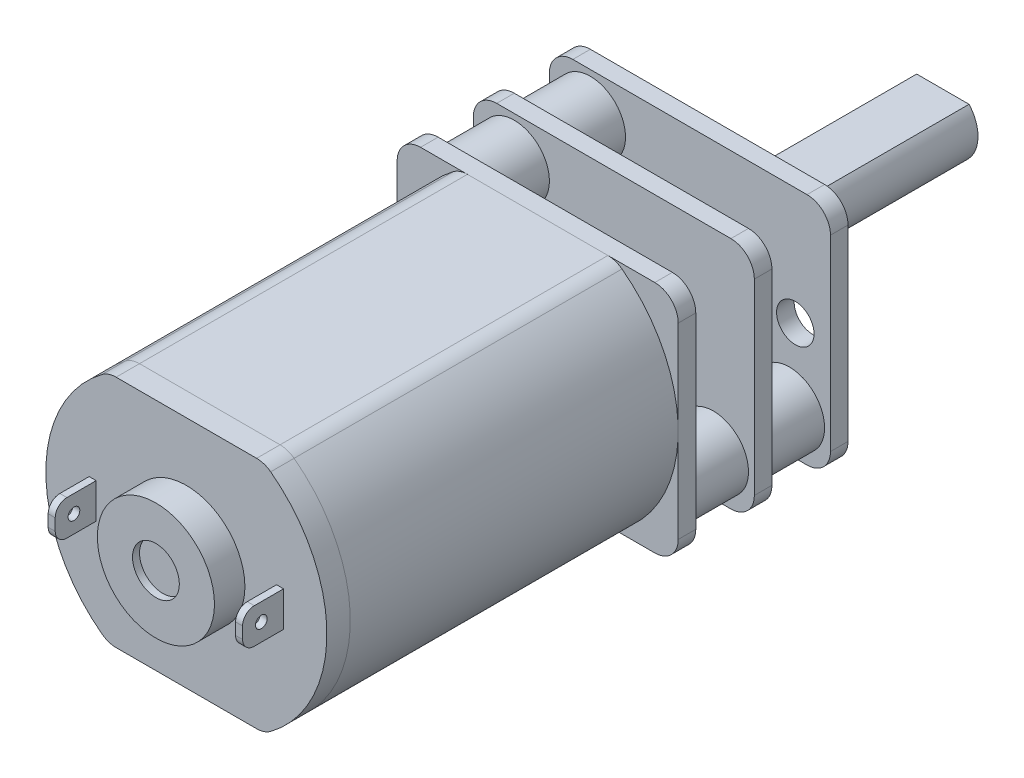
SolidWorks part; units mm, degrees
ref_plane "Front Plane" through (0, 0, 0) normal (0, 0, 1) x (1, 0, 0)
ref_plane "Top Plane" through (0, 0, 0) normal (0, 1, 0) x (1, 0, 0)
ref_plane "Right Plane" through (0, 0, 0) normal (1, 0, 0) x (0, 0, -1)
sketch "Sketch1" plane through (0, 0, 0) normal (0, 0, 1) x (1, 0, 0)
  line L0 (-6, 0) -> (6, 0) construction
  line L1 (-3.3166, -5) -> (3.3166, -5)
  line L2 (-3.3166, 5) -> (3.3166, 5)
  line L4 (-6, 5) -> (6, 5) construction
  line L5 (-6, -5) -> (6, -5) construction
  arc A0 (-3.3166, 5) -> (-3.3166, -5) centre (0, 0) ccw
  arc A1 (3.3166, -5) -> (3.3166, 5) centre (0, 0) ccw
  dimension "D1" = 12
  dimension "D2" = 5
  dimension "D3" = 5
extrude "Boss-Extrude1" add sketch "Sketch1" against normal blind 14
fillet "Fillet1" radius 1 4 edges at (3.3166, -5, -7) (-3.3166, -5, -7) (3.3166, 5, -7) (-3.3166, 5, -7)
sketch "Sketch2" plane through (0, 0, 0) normal (0, 0, 1) x (1, 0, 0)
  line L2 (-3, -5) -> (3, -5)
  line L3 (3, 5) -> (-3, 5)
  line L4 (-3, -5) -> (3, -5)
  line L5 (3, 5) -> (-3, 5)
  arc A6 (3, -5) -> (3.6, -4.8) centre (3, -4) ccw
  arc A7 (3.6, -4.8) -> (3.6, 4.8) centre (0, 0) ccw
  arc A8 (3.6, 4.8) -> (3, 5) centre (3, 4) ccw
  arc A9 (-3, 5) -> (-3.6, 4.8) centre (-3, 4) ccw
  arc A10 (-3.6, 4.8) -> (-3.6, -4.8) centre (0, 0) ccw
  arc A11 (-3.6, -4.8) -> (-3, -5) centre (-3, -4) ccw
  arc A12 (3, -5) -> (3.6, -4.8) centre (3, -4) ccw
  arc A13 (3.6, -4.8) -> (3.6, 4.8) centre (0, 0) ccw
  arc A14 (3.6, 4.8) -> (3, 5) centre (3, 4) ccw
  arc A15 (-3, 5) -> (-3.6, 4.8) centre (-3, 4) ccw
  arc A16 (-3.6, 4.8) -> (-3.6, -4.8) centre (0, 0) ccw
  arc A17 (-3.6, -4.8) -> (-3, -5) centre (-3, -4) ccw
  dimension "D1" = 0
extrude "Boss-Extrude2" add sketch "Sketch2" along normal blind 1 separate body
sketch "Sketch3" plane through (0, 0, 1) normal (0, 0, 1) x (1, 0, 0)
  circle A0 centre (0, 0) radius 2.5
  dimension "D1" = 5
extrude "Boss-Extrude3" add sketch "Sketch3" along normal blind 1.3
sketch "Sketch4" plane through (0, 0, 2.3) normal (0, 0, 1) x (1, 0, 0)
  circle A0 centre (0, 0) radius 1
  dimension "D1" = 2
extrude "Cut-Extrude1" cut sketch "Sketch4" against normal blind 0.3
sketch "Sketch5" plane through (0, 0, 1) normal (0, 0, 1) x (1, 0, 0)
  line L0 (-6, 0) -> (6, 0) construction
  line L1 (0, 5) -> (0, -5) construction
  line L2 (-4.15, 0.75) -> (-3.85, 0.75)
  line L3 (-4.15, 0.75) -> (-4.15, -0.75)
  line L4 (-4.15, -0.75) -> (-3.85, -0.75)
  line L5 (-3.85, 0.75) -> (-3.85, -0.75)
  line L6 (-4.15, 0.75) -> (-3.85, -0.75) construction
  line L7 (-4.15, -0.75) -> (-3.85, 0.75) construction
  line L8 (3, 5) -> (-3, 5) construction
  line L9 (-3, -5) -> (3, -5) construction
  line L10 (4.15, -0.75) -> (3.85, 0.75) construction
  line L11 (4.15, 0.75) -> (3.85, -0.75) construction
  line L12 (3.85, 0.75) -> (3.85, -0.75)
  line L13 (4.15, -0.75) -> (3.85, -0.75)
  line L14 (4.15, 0.75) -> (4.15, -0.75)
  line L15 (4.15, 0.75) -> (3.85, 0.75)
  arc A0 (-3.6, 4.8) -> (-3.6, -4.8) centre (0, 0) ccw construction
  arc A1 (3.6, -4.8) -> (3.6, 4.8) centre (0, 0) ccw construction
  point P8 (-4, 0)
  point P13 (-4, 0.75)
  point P20 (0, 0)
  point P25 (4, 0)
  dimension "D1" = 1.5
  dimension "D2" = 0.3
  dimension "D3" = 4
extrude "Boss-Extrude4" add sketch "Sketch5" along normal blind 1.75
fillet "Fillet2" radius 0.5 4 edges at (4, 0.75, 2.75) (4, -0.75, 2.75) (-4, -0.75, 2.75) (-4, 0.75, 2.75)
sketch "Sketch6" plane through (-4.15, 0, 0) normal (-1, 0, 0) x (0, 0, 1)
  line L0 (2.75, 0.25) -> (2.75, -0.25) construction
  line L1 (2.25, 0.75) -> (1, 0.75) construction
  circle A0 centre (1.95, 0) radius 0.25
  point P4 (2.75, 0)
  dimension "D1" = 0.5
  dimension "D2" = 0.8
  dimension "D3" = 0.75
extrude "Cut-Extrude2" cut sketch "Sketch6" against normal up to surface (0.3 mm away) up to face at (-3.85, 0, 2.0345)
sketch "Sketch7" plane through (4.15, 0, 0) normal (1, 0, 0) x (0, 0, -1)
  circle A0 centre (-1.95, 0) radius 0.25 construction
  circle A1 centre (-1.95, 0) radius 0.25
extrude "Cut-Extrude3" cut sketch "Sketch7" against normal up to surface (0.3 mm away) up to face at (3.85, 0, 2.0345)
sketch "Sketch8" plane through (0, 0, -14) normal (0, 0, -1) x (-1, 0, 0)
  line L0 (-3, 5) -> (3, 5) construction
  line L1 (-6, 5) -> (6, 5)
  line L2 (3, -5) -> (-3, -5) construction
  line L3 (6, -5) -> (-6, -5)
  line L4 (-6, 5) -> (-6, -5)
  line L5 (6, 5) -> (6, -5)
  arc A0 (3.6, -4.8) -> (3.6, 4.8) centre (0, 0) ccw construction
  arc A1 (-3.6, 4.8) -> (-3.6, -4.8) centre (0, 0) ccw construction
  arc A2 (-3.6, 4.8) -> (-3.6, -4.8) centre (0, 0) ccw construction
  point P11 (6, 0)
extrude "Boss-Extrude5" add sketch "Sketch8" along normal blind 0.75 separate body
ref_plane "Plane1" through (0, 0, -17.25) normal (0, 0, -1) x (-1, 0, 0)
sketch "Sketch9" plane through (0, 0, -17.25) normal (0, 0, -1) x (-1, 0, 0)
  line L4 (-6, 5) -> (-6, -5)
  line L5 (-6, -5) -> (6, -5)
  line L6 (6, -5) -> (6, 5)
  line L7 (6, 5) -> (-6, 5)
  line L8 (-6, 5) -> (-6, -5)
  line L9 (-6, -5) -> (6, -5)
  line L10 (6, -5) -> (6, 5)
  line L11 (6, 5) -> (-6, 5)
  dimension "D1" = 0
extrude "Boss-Extrude6" add sketch "Sketch9" along normal blind 0.75 separate body
ref_plane "Plane2" through (0, 0, -20.5) normal (0, 0, -1) x (-1, 0, 0)
sketch "Sketch10" plane through (0, 0, -20.5) normal (0, 0, -1) x (-1, 0, 0)
  line L4 (6, 5) -> (-6, 5)
  line L5 (-6, 5) -> (-6, -5)
  line L6 (-6, -5) -> (6, -5)
  line L7 (6, -5) -> (6, 5)
  line L8 (6, 5) -> (-6, 5)
  line L9 (-6, 5) -> (-6, -5)
  line L10 (-6, -5) -> (6, -5)
  line L11 (6, -5) -> (6, 5)
  dimension "D1" = 0
extrude "Boss-Extrude7" add sketch "Sketch10" along normal blind 0.75 separate body
sketch "Sketch11" plane through (0, 0, -21.25) normal (0, 0, -1) x (-1, 0, 0)
  line L0 (-6, 5) -> (-6, -5) construction
  line L1 (-6, -5) -> (6, -5) construction
  line L2 (6, -5) -> (6, 5) construction
  line L3 (6, 5) -> (-6, 5) construction
  circle A0 centre (4.25, 3.25) radius 1.5
  circle A1 centre (-4.25, -3.25) radius 1.5
  dimension "D1" = 3
  dimension "D2" = 3
  dimension "D3" = 1.75
  dimension "D4" = 1.75
  dimension "D5" = 1.75
  dimension "D6" = 1.75
extrude "Boss-Extrude8" add sketch "Sketch11" against normal up to surface (6.2 mm away) from offset 0.3 separate body up to face at (0, 0, -14.75) offset against normal yes
fillet "Fillet3" radius 1 4 edges at (-6, 5, -20.875) (6, -5, -20.875) (-6, -5, -20.875) (6, 5, -20.875)
fillet "Fillet4" radius 1 4 edges at (6, -5, -17.625) (6, 5, -17.625) (-6, 5, -17.625) (-6, -5, -17.625)
fillet "Fillet5" radius 1 4 edges at (-6, -5, -14.375) (-6, 5, -14.375) (6, -5, -14.375) (6, 5, -14.375)
sketch "Sketch12" plane through (0, 0, -21.25) normal (0, 0, -1) x (-1, 0, 0)
  circle A0 centre (0, 0) radius 2
  dimension "D1" = 4
extrude "Boss-Extrude9" add sketch "Sketch12" along normal blind 0.8
sketch "Sketch13" plane through (0, 0, -22.05) normal (0, 0, -1) x (-1, 0, 0)
  circle A0 centre (0, 0) radius 1.5
  dimension "D1" = 3
extrude "Boss-Extrude10" add sketch "Sketch13" along normal blind 9.25
ref_plane "Plane3" through (0, 1.5, 0) normal (0, 1, 0) x (0, 0, 1)
sketch "Sketch14" plane through (0, 1.5, 0) normal (0, 1, 0) x (0, 0, 1)
  line L0 (-22.05, 0) -> (-31.3, 0)
  line L1 (-22.05, 0) -> (-31.3, 0) construction
  line L2 (-22.05, 1.5) -> (-31.3, 1.5)
  line L3 (-22.05, -1.5) -> (-31.3, -1.5)
  line L5 (-22.05, 1.5) -> (-22.05, -1.5)
  line L6 (-31.3, 1.5) -> (-31.3, -1.5)
  dimension "D1" = 1.5
  dimension "D2" = 1.5
extrude "Cut-Extrude4" cut sketch "Sketch14" against normal blind 0.5
sketch "Sketch15" plane through (0, 0, -21.25) normal (0, 0, -1) x (-1, 0, 0)
  line L0 (-4.25, -1.75) -> (-4.25, -4.75) construction
  line L1 (-5.75, -3.25) -> (-2.75, -3.25) construction
  line L2 (-4.45, -1.7634) -> (-4.45, -2.85)
  line L3 (-4.05, -1.7634) -> (-4.05, -2.85)
  line L4 (-3.85, -3.45) -> (-2.7634, -3.45)
  line L11 (-3.85, -3.05) -> (-2.7634, -3.05)
  line L12 (-5.7366, -3.45) -> (-4.65, -3.45)
  line L13 (-5.7366, -3.05) -> (-4.65, -3.05)
  line L14 (4.25, 4.75) -> (4.25, 1.75) construction
  line L15 (2.75, 3.25) -> (5.75, 3.25) construction
  line L16 (4.05, 4.7366) -> (4.05, 3.65)
  line L17 (4.45, 4.7366) -> (4.45, 3.65)
  line L18 (2.7634, 3.05) -> (3.85, 3.05)
  line L19 (2.7634, 3.45) -> (3.85, 3.45)
  line L20 (4.05, 2.85) -> (4.05, 1.7634)
  line L21 (4.45, 2.85) -> (4.45, 1.7634)
  line L22 (4.65, 3.05) -> (5.7366, 3.05)
  line L23 (4.65, 3.45) -> (5.7366, 3.45)
  line L24 (-5.75, -3.05) -> (-2.75, -3.05) construction
  line L25 (-5.75, -3.45) -> (-2.75, -3.45) construction
  line L26 (-4.45, -3.65) -> (-4.45, -4.7366)
  line L27 (-4.05, -3.65) -> (-4.05, -4.7366)
  line L28 (-4.45, -1.75) -> (-4.45, -4.75) construction
  line L30 (-4.05, -1.75) -> (-4.05, -4.75) construction
  circle A0 centre (-4.25, -3.25) radius 1.5 construction
  circle A1 centre (4.25, 3.25) radius 1.5
  circle A2 centre (4.25, 3.25) radius 1.5
  circle A3 centre (-4.25, -3.25) radius 1.5
  arc A4 (-4.45, -3.65) -> (-4.65, -3.45) centre (-4.65, -3.65) ccw
  arc A5 (-4.05, -3.65) -> (-3.85, -3.45) centre (-3.85, -3.65) cw
  arc A6 (-3.85, -3.05) -> (-4.05, -2.85) centre (-3.85, -2.85) cw
  arc A7 (-4.65, -3.05) -> (-4.45, -2.85) centre (-4.65, -2.85) ccw
  arc A8 (4.05, 2.85) -> (3.85, 3.05) centre (3.85, 2.85) ccw
  arc A9 (4.65, 3.05) -> (4.45, 2.85) centre (4.65, 2.85) ccw
  arc A10 (4.45, 3.65) -> (4.65, 3.45) centre (4.65, 3.65) ccw
  arc A11 (4.05, 3.65) -> (3.85, 3.45) centre (3.85, 3.65) cw
  point P14 (-4.05, -3.45)
  point P61 (4.45, 3.45)
  dimension "D2" = 0.2
  dimension "D7" = 0.2
  dimension "D1" = 0
  dimension "D3" = 0.2
  dimension "D4" = 0.2
  dimension "D5" = 0.2
  dimension "D6" = 0.2
extrude "Cut-Extrude5" cut sketch "Sketch15" against normal blind 0.25
sketch "Sketch16" plane through (0, 0, -21.25) normal (0, 0, -1) x (-1, 0, 0)
  circle A0 centre (4.25, 3.25) radius 1.5 construction
  circle A1 centre (4.25, 3.25) radius 1.5
  circle A2 centre (-4.25, -3.25) radius 1.5 construction
  circle A3 centre (-4.25, -3.25) radius 1.5
extrude "Cut-Extrude6" cut sketch "Sketch16" against normal blind 0.05
sketch "Sketch17" plane through (0, 0, -21.25) normal (0, 0, -1) x (-1, 0, 0)
  line L0 (-6, 0) -> (6, 0) construction
  line L1 (-6, 4) -> (-6, -4) construction
  line L2 (6, -4) -> (6, 4) construction
  circle A0 centre (-4.5, 0) radius 0.8
  circle A1 centre (4.5, 0) radius 0.8
  dimension "D1" = 1.6
  dimension "D2" = 1.6
  dimension "D3" = 4.5
  dimension "D4" = 4.5
extrude "Cut-Extrude7" cut sketch "Sketch17" against normal up to surface (0.75 mm away) up to face at (0, 0, -20.5)
